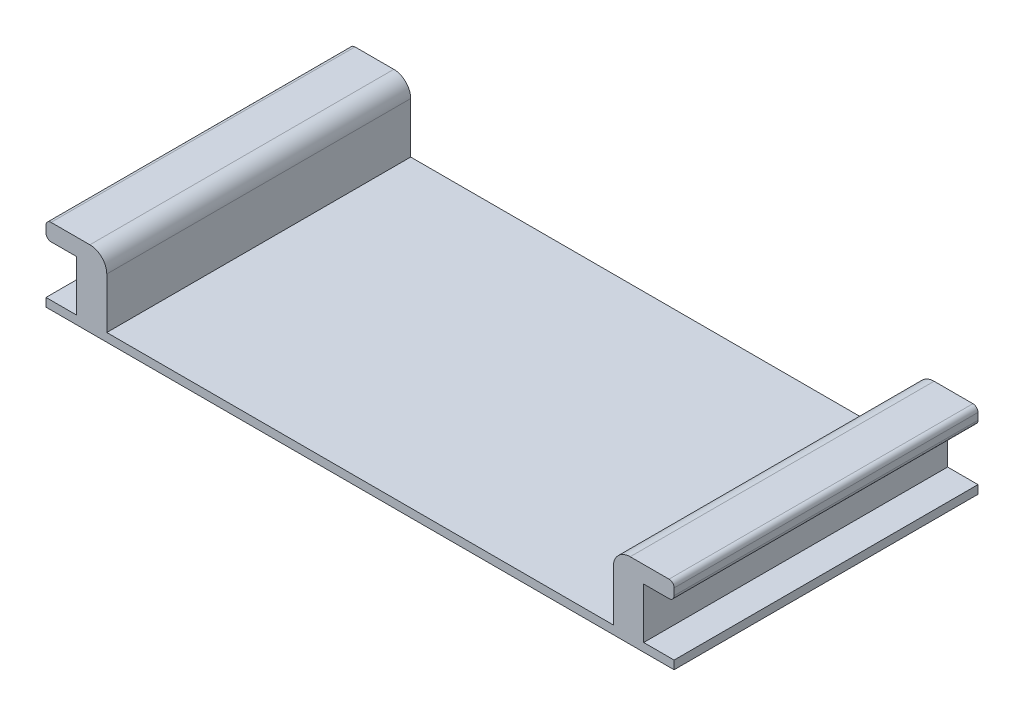
SolidWorks part; units mm, degrees
ref_plane "Front Plane" through (0, 0, 0) normal (0, 0, 1) x (1, 0, 0)
ref_plane "Top Plane" through (0, 0, 0) normal (0, 1, 0) x (1, 0, 0)
ref_plane "Right Plane" through (0, 0, 0) normal (1, 0, 0) x (0, 0, -1)
sketch "Sketch1" plane through (0, 0, 0) normal (0, 0, 1) x (1, 0, 0)
  line L0 (-15, 0) -> (-15, 4)
  line L1 (-18.6, -0.5) -> (18.6, -0.5)
  line L2 (-18.6, -0.5) -> (-18.6, 0)
  line L3 (-18.6, 0) -> (-16.8, 0)
  line L4 (18.6, -0.5) -> (18.6, 0)
  line L5 (-15, 4) -> (-18.6, 4)
  line L6 (-18.6, 4) -> (-18.6, 3)
  line L7 (-18.6, 3) -> (-16.8, 3)
  line L8 (-16.8, 3) -> (-16.8, 0)
  line L10 (0, 0) -> (0, -0.5) construction
  line L11 (-15, 0) -> (15, 0)
  line L12 (15, 0) -> (15, 4)
  line L13 (16.8, 3) -> (16.8, 0)
  line L14 (18.6, 3) -> (16.8, 3)
  line L15 (18.6, 4) -> (18.6, 3)
  line L16 (15, 4) -> (18.6, 4)
  line L17 (16.8, 0) -> (18.6, 0)
  line L18 (-16.8, 0) -> (-15, 0) construction
  point P10 (-16.8, 4)
  dimension "D1" = 0.5
  dimension "D2" = 3
  dimension "D3" = 1
  dimension "D4" = 15
  dimension "D5" = 1.8
extrude "Boss-Extrude1" add sketch "Sketch1" along normal blind 18
fillet "Fillet1" radius 1 2 edges at (-15, 4, 9) (15, 4, 9)
fillet "Fillet2" radius 0.3 4 edges at (-18.6, 3, 9) (-18.6, 4, 9) (18.6, 3, 9) (18.6, 4, 9)
